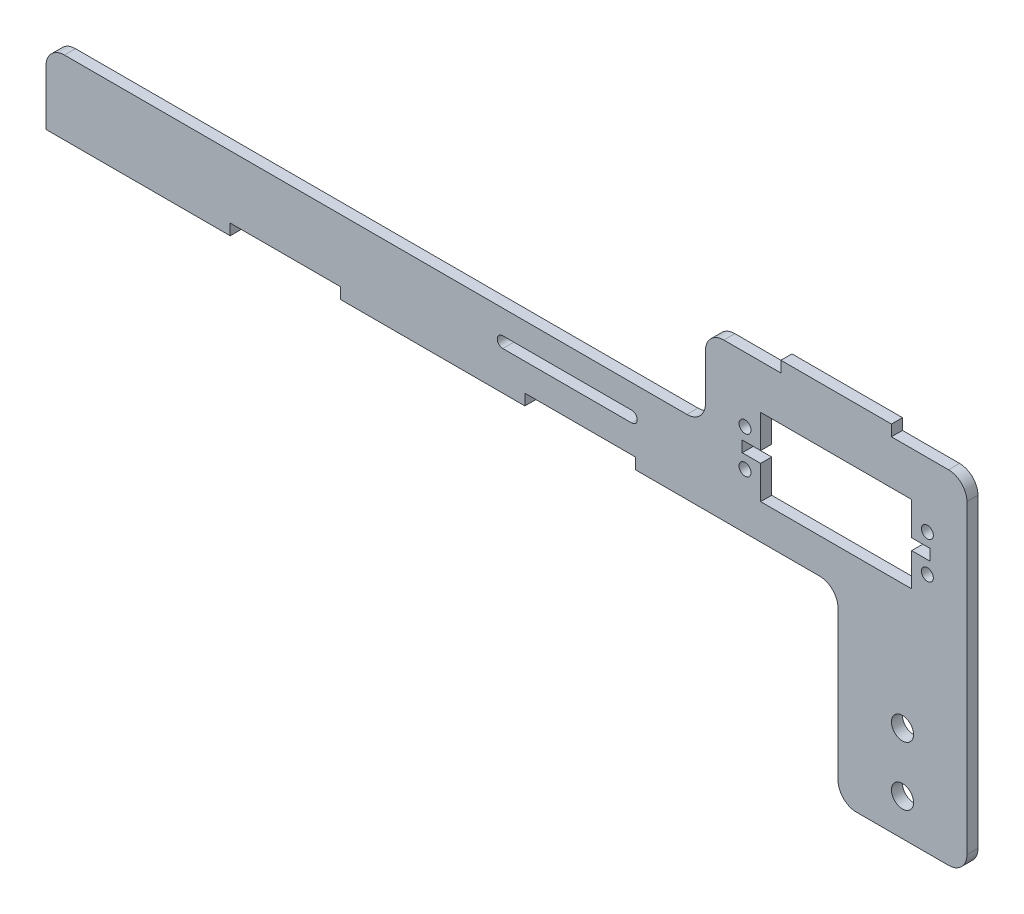
SolidWorks part; units mm, degrees
material "ACM"
ref_plane "Plano frontal" through (0, 0, 0) normal (0, 0, 1) x (1, 0, 0)
ref_plane "Plano superior" through (0, 0, 0) normal (0, 1, 0) x (1, 0, 0)
ref_plane "Plano direito" through (0, 0, 0) normal (1, 0, 0) x (0, 0, -1)
sketch "Esboço1" plane through (0, 0, 0) normal (0, 0, 1) x (1, 0, 0)
  line L0 (194, 0) -> (235, 0) construction
  line L1 (215, -20) -> (160, -20)
  line L2 (250, -20) -> (250, 22.5)
  line L4 (0, -20) -> (0, 0)
  line L5 (194, 10.5) -> (235, 10.5)
  line L6 (194, 10.5) -> (194, -10.5)
  line L7 (194, -10.5) -> (235, -10.5)
  line L8 (235, 10.5) -> (235, -10.5)
  line L9 (214.5, 10.5) -> (214.5, -10.5) construction
  line L10 (0, 0) -> (179, 0)
  line L11 (179, 0) -> (179, 22.5)
  line L12 (250, 0) -> (184.4373, 0) construction
  line L13 (50, -20) -> (50, -17)
  line L14 (50, -17) -> (80, -17)
  line L15 (80, -17) -> (80, -20)
  line L16 (130, -20) -> (130, -17)
  line L17 (130, -17) -> (160, -17)
  line L18 (160, -17) -> (160, -20)
  line L19 (50, -20) -> (0, -20)
  line L20 (130, -20) -> (80, -20)
  line L21 (124, -8) -> (159, -8) construction
  line L22 (124, -6.5) -> (159, -6.5)
  line L23 (124, -9.5) -> (159, -9.5)
  line L26 (215, -20) -> (215, -70.5)
  line L27 (215, -70.5) -> (250, -70.5)
  line L28 (250, -20) -> (250, -70.5)
  line L29 (194, 1.5) -> (189, 1.5)
  line L30 (189, 1.5) -> (189, -1.5)
  line L31 (189, -1.5) -> (194, -1.5)
  line L32 (235, 1.5) -> (240, 1.5)
  line L33 (240, 1.5) -> (240, -1.5)
  line L34 (240, -1.5) -> (235, -1.5)
  line L36 (229.5, 25.5) -> (199.5, 25.5)
  line L37 (229.5, 25.5) -> (229.5, 22.5)
  line L38 (229.5, 22.5) -> (199.5, 22.5)
  line L39 (199.5, 25.5) -> (199.5, 22.5)
  line L40 (229.5, 25.5) -> (199.5, 22.5) construction
  line L41 (229.5, 22.5) -> (199.5, 25.5) construction
  line L42 (179, 22.5) -> (250, 22.5)
  circle A0 centre (189.75, 5) radius 1.625
  circle A1 centre (239.25, 5) radius 1.625
  circle A2 centre (239.25, -5) radius 1.625
  circle A3 centre (189.75, -5) radius 1.625
  arc A5 (124, -6.5) -> (124, -9.5) centre (124, -8) ccw
  arc A6 (159, -9.5) -> (159, -6.5) centre (159, -8) ccw
  circle A7 centre (232.5, -60.5) radius 3
  circle A8 centre (232.5, -44.5) radius 3
  point P36 (141.5, -8)
  point P51 (189, 0)
  point P57 (214.5, 24)
  point P62 (214.5, 20)
  dimension "D8" = 3.25
  dimension "D9" = 10
  dimension "D19" = 1.5
  dimension "D27" = 6
  dimension "D29" = 10
  dimension "D30" = 6
  dimension "D3" = 41
  dimension "D4" = 15
  dimension "D5" = 21
  dimension "D6" = 35
  dimension "D7" = 49.5
  dimension "D10" = 20
  dimension "D11" = 15
  dimension "D12" = 179
  dimension "D13" = 50
  dimension "D14" = 30
  dimension "D15" = 3
  dimension "D16" = 50
  dimension "D17" = 30
  dimension "D18" = 3
  dimension "D20" = 8
  dimension "D21" = 35
  dimension "D22" = 20
  dimension "D23" = 12
  dimension "D25" = 9.5
  dimension "D28" = 50.5
  dimension "D31" = 16
  dimension "D32" = 3
  dimension "D33" = 5
  dimension "D34" = 3
  dimension "D35" = 30
extrude "Ressalto-extrusão1" add sketch "Esboço1" along normal blind 3
fillet "Filete1" radius 5 7 edges at (250, 22.5, 1.5) (250, -70.5, 1.5) (215, -70.5, 1.5) (215, -20, 1.5) (0, 0, 1.5) (179, 0, 1.5) (179, 22.5, 1.5)
